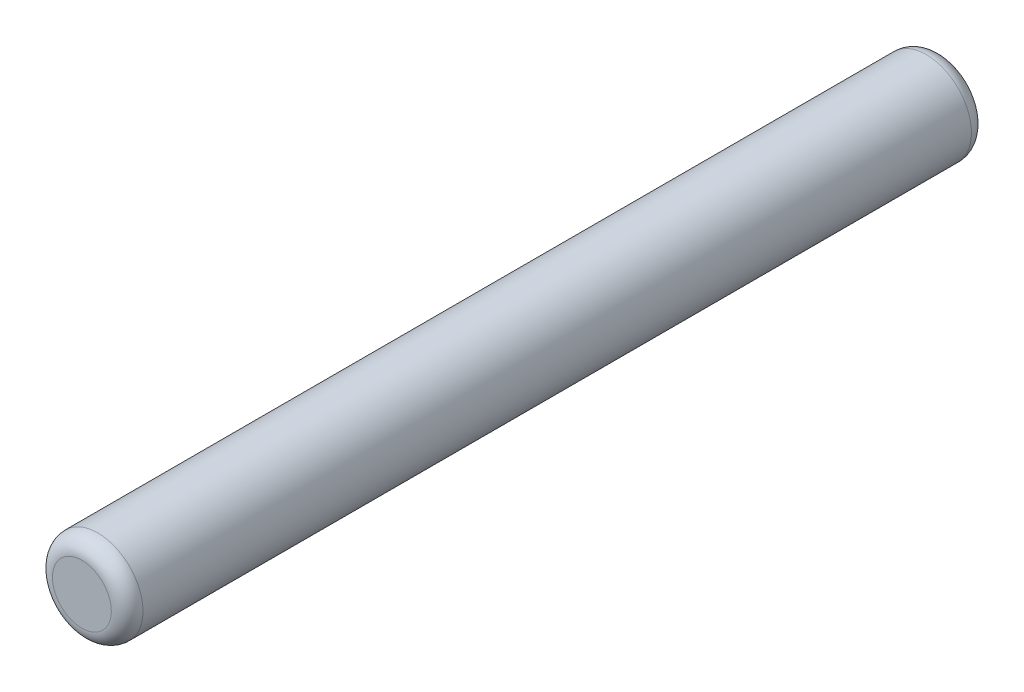
SolidWorks part; units mm, degrees
ref_plane "Front" through (0, 0, 0) normal (0, 0, 1) x (1, 0, 0)
ref_plane "Top" through (0, 0, 0) normal (0, 1, 0) x (1, 0, 0)
ref_plane "Right" through (0, 0, 0) normal (1, 0, 0) x (0, 0, -1)
sketch "Sketch1" plane through (0, 0, 0) normal (0, 0, 1) x (1, 0, 0)
  circle A0 centre (0, 0) radius 1
  dimension "D1" = 2
extrude "Boss-Extrude1" add sketch "Sketch1" along normal mid plane 19
fillet "Fillet1" radius 0.35 2 edges at (1, 0, -9.5) (1, 0, 9.5)
